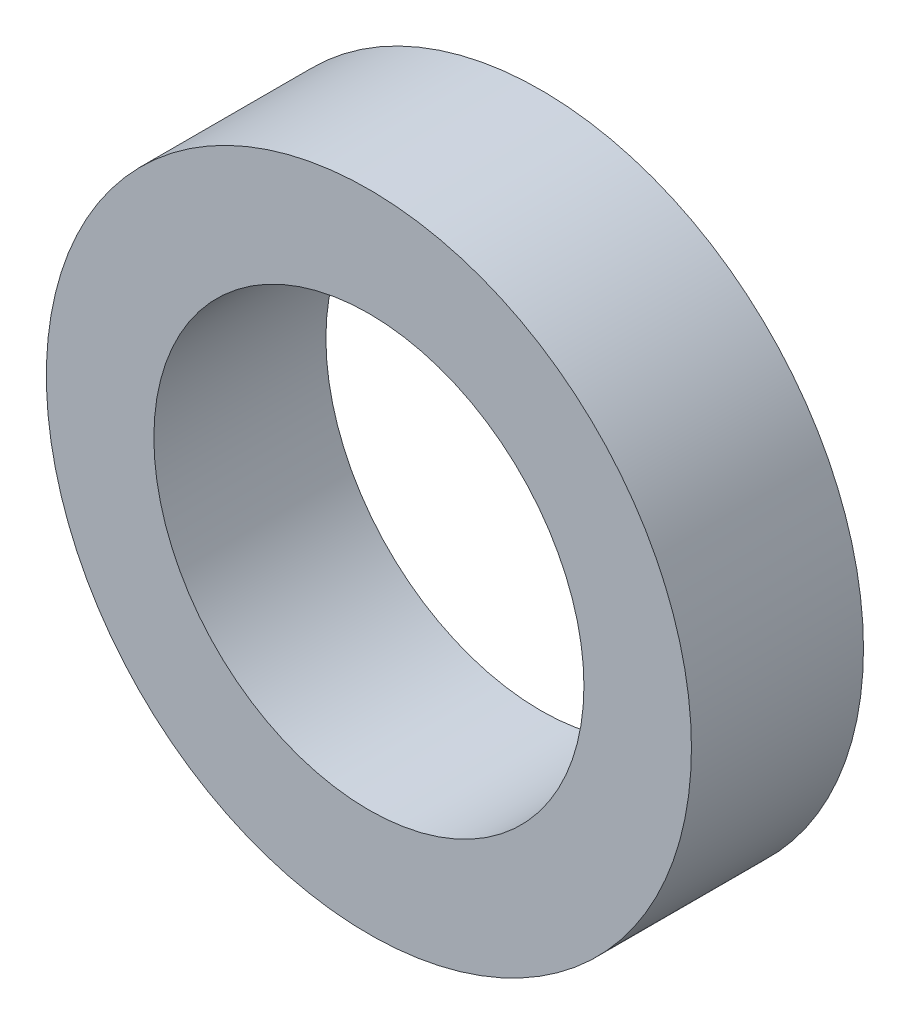
SolidWorks part; units mm, degrees
ref_plane "前视基准面" through (0, 0, 0) normal (0, 0, 1) x (1, 0, 0)
ref_plane "上视基准面" through (0, 0, 0) normal (0, 1, 0) x (1, 0, 0)
ref_plane "右视基准面" through (0, 0, 0) normal (1, 0, 0) x (0, 0, -1)
sketch "草图1" plane through (0, 0, 0) normal (0, 0, 1) x (1, 0, 0)
  circle A0 centre (0, 0) radius 5
  circle A1 centre (0, 0) radius 7.5
extrude "凸台-拉伸1" add sketch "草图1" along normal blind 4
